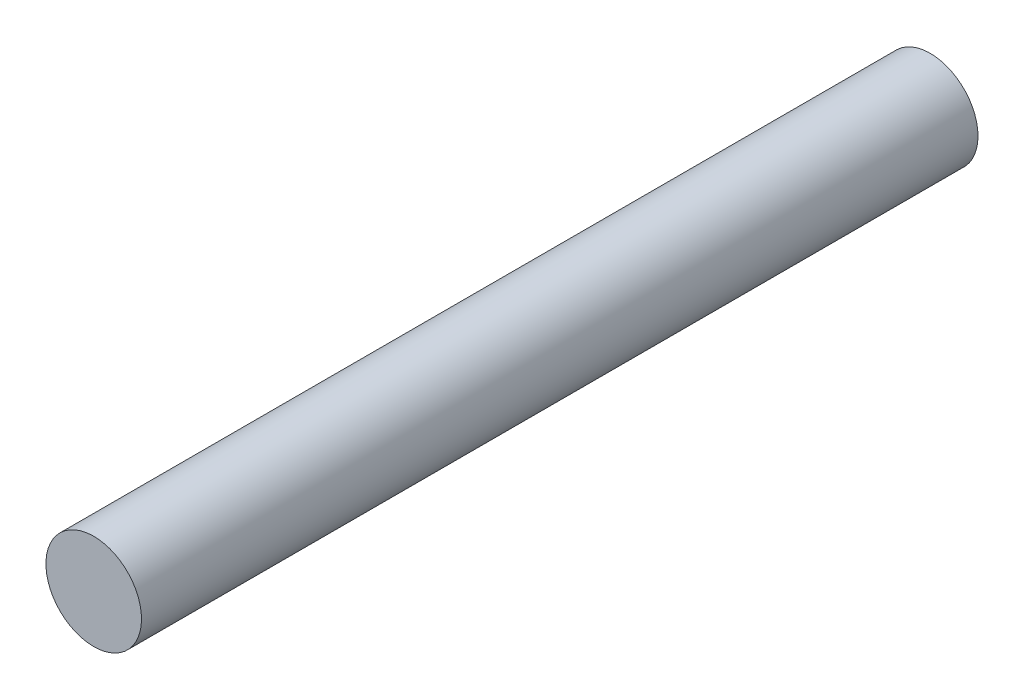
SolidWorks part; units mm, degrees
material "6061 合金"
ref_plane "前视基准面" through (0, 0, 0) normal (0, 0, 1) x (1, 0, 0)
ref_plane "上视基准面" through (0, 0, 0) normal (0, 1, 0) x (1, 0, 0)
ref_plane "右视基准面" through (0, 0, 0) normal (1, 0, 0) x (0, 0, -1)
sketch "草图1" plane through (0, 0, 0) normal (0, 0, 1) x (1, 0, 0)
  circle A0 centre (0, 0) radius 4
  dimension "D1" = 8
extrude "凸台-拉伸1" add sketch "草图1" along normal blind 70
sketch "草图2" plane through (0, 0, 70) normal (0, 0, 1) x (1, 0, 0)
  line L0 (0, 0) -> (0, 13.6972) construction
